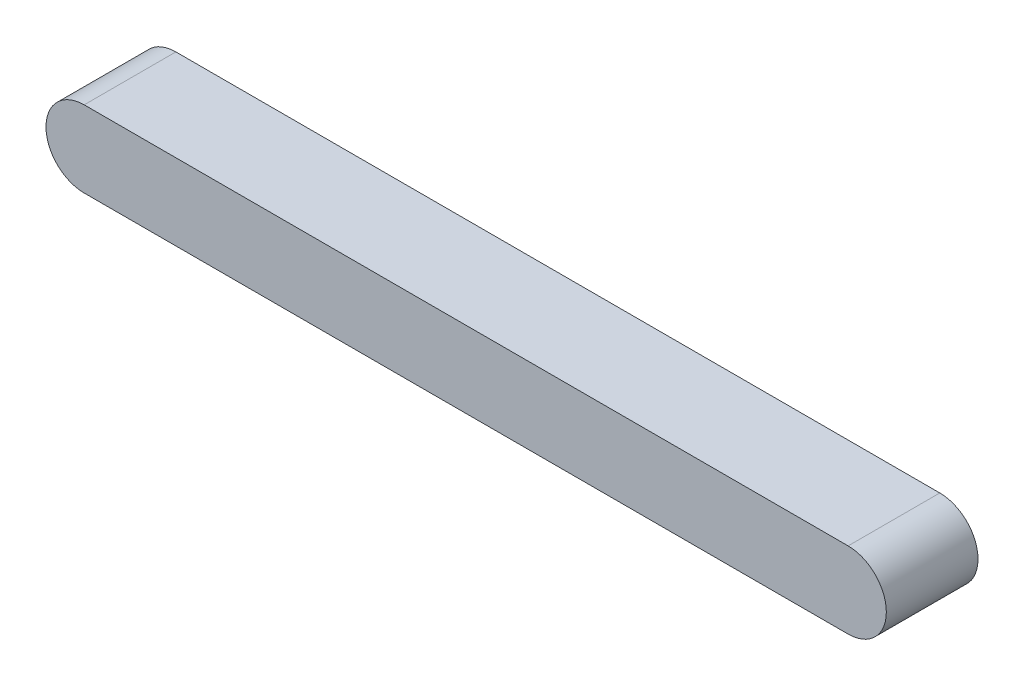
SolidWorks part; units mm, degrees
ref_plane "前视基准面" through (0, 0, 0) normal (0, 0, 1) x (1, 0, 0)
ref_plane "上视基准面" through (0, 0, 0) normal (0, 1, 0) x (1, 0, 0)
ref_plane "右视基准面" through (0, 0, 0) normal (1, 0, 0) x (0, 0, -1)
sketch "草图1" plane through (0, 0, 0) normal (0, 0, 1) x (1, 0, 0)
  line L1 (-50, 5) -> (50, 5)
  line L2 (-50, -5) -> (50, -5)
  arc A0 (-50, 5) -> (-50, -5) centre (-50, 0) ccw
  arc A1 (50, -5) -> (50, 5) centre (50, 0) ccw
  point P4 (0, 0)
  dimension "D2" = 10
  dimension "D3" = 10
  dimension "D1" = 100
extrude "凸台-拉伸1" add sketch "草图1" along normal blind 12
